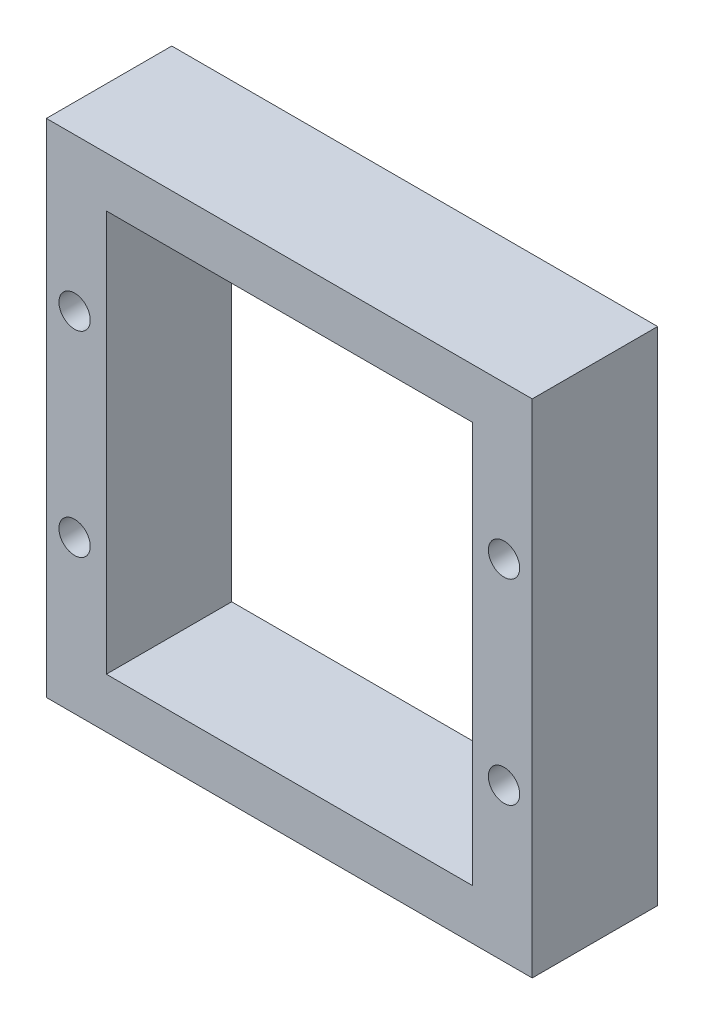
SolidWorks part; units mm, degrees
ref_plane "Front Plane" through (0, 0, 0) normal (0, 0, 1) x (1, 0, 0)
ref_plane "Top Plane" through (0, 0, 0) normal (0, 1, 0) x (1, 0, 0)
ref_plane "Right Plane" through (0, 0, 0) normal (1, 0, 0) x (0, 0, -1)
sketch "Sketch1" plane through (0, 0, 0) normal (0, 0, 1) x (1, 0, 0)
  line L1 (-15.5, -16) -> (15.5, -16)
  line L2 (-15.5, -16) -> (-15.5, 16)
  line L3 (-15.5, 16) -> (15.5, 16)
  line L4 (15.5, -16) -> (15.5, 16)
  line L5 (-15.5, -16) -> (15.5, 16) construction
  line L6 (-15.5, 16) -> (15.5, -16) construction
  point P0 (0, 0)
  dimension "D1" = 31
  dimension "D2" = 32
extrude "Boss-Extrude1" add sketch "Sketch1" along normal blind 8
sketch "Sketch2" plane through (0, 0, 8) normal (0, 0, 1) x (1, 0, 0)
  line L1 (-11.675, -12.8) -> (11.675, -12.8)
  line L2 (-11.675, -12.8) -> (-11.675, 12.8)
  line L3 (-11.675, 12.8) -> (11.675, 12.8)
  line L4 (11.675, -12.8) -> (11.675, 12.8)
  line L5 (-11.675, -12.8) -> (11.675, 12.8) construction
  line L6 (-11.675, 12.8) -> (11.675, -12.8) construction
  point P0 (0, 0)
  dimension "D1" = 23.35
  dimension "D2" = 25.6
extrude "Cut-Extrude1" cut sketch "Sketch2" against normal blind 13
sketch "Sketch3" plane through (0, 0, 8) normal (0, 0, 1) x (1, 0, 0)
  line L0 (0, -4.4) -> (0, 4.4) construction
  circle A0 centre (13.7, 6.25) radius 1
  circle A3 centre (13.7, -6.25) radius 1
  circle A4 centre (-13.7, -6.25) radius 1
  circle A5 centre (-13.7, 6.25) radius 1
  dimension "D1" = 2
  dimension "D2" = 2
extrude "Cut-Extrude2" cut sketch "Sketch3" against normal blind 10
